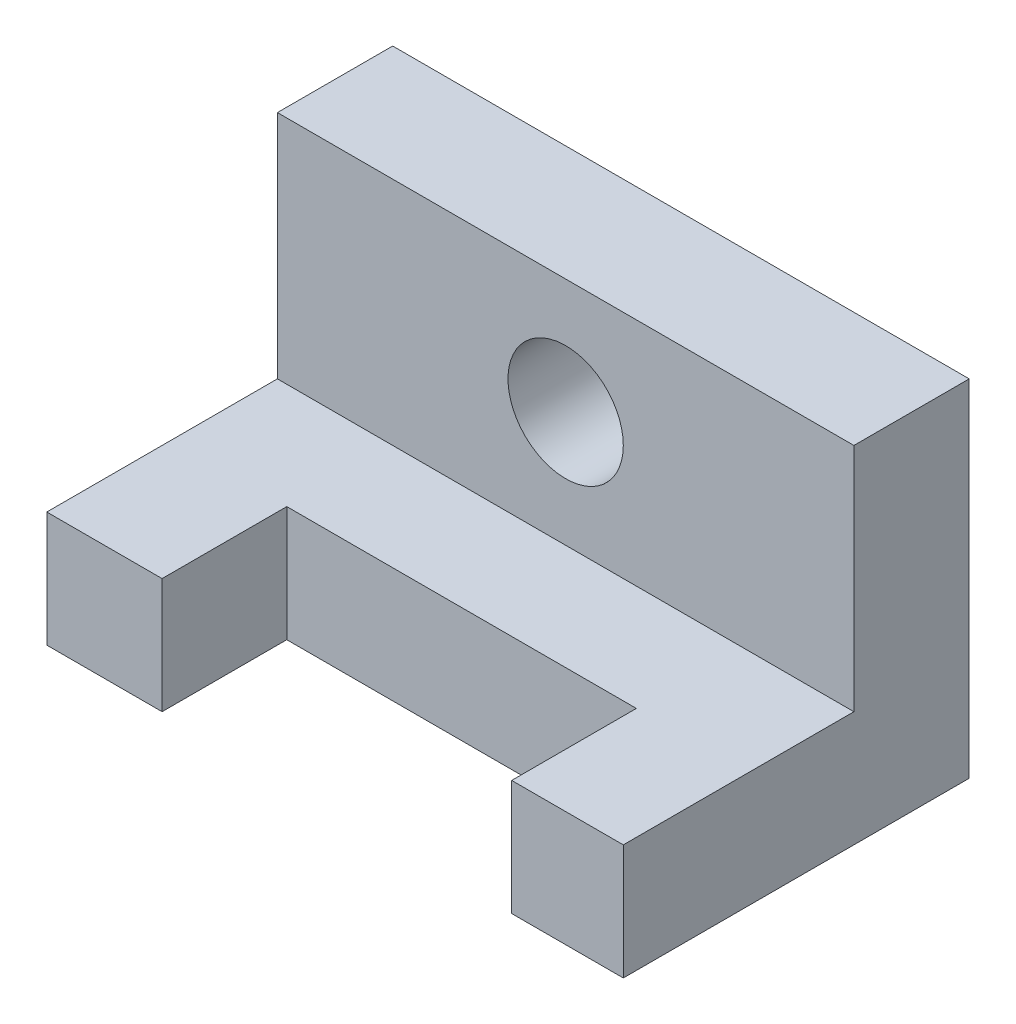
SolidWorks part; units mm, degrees
material "1060 Alloy"
ref_plane "Front Plane" through (0, 0, 0) normal (0, 0, 1) x (1, 0, 0)
ref_plane "Top Plane" through (0, 0, 0) normal (0, 1, 0) x (1, 0, 0)
ref_plane "Right Plane" through (0, 0, 0) normal (1, 0, 0) x (0, 0, -1)
sketch "Sketch1" plane through (0, 0, 0) normal (1, 0, 0) x (0, 0, -1)
  line L1 (0, 0) -> (-1524, 0)
  line L2 (0, 0) -> (0, 1524)
  line L3 (0, 1524) -> (-508, 1524)
  line L4 (-1524, 0) -> (-1524, 508)
  line L7 (-1524, 508) -> (-508, 508)
  line L8 (-508, 1524) -> (-508, 508)
  dimension "D1" = 1524
  dimension "D2" = 1524
  dimension "D3" = 1016
  dimension "D4" = 1016
extrude "Boss-Extrude1" add sketch "Sketch1" along normal blind 2540
sketch "Sketch2" plane through (0, 0, 0) normal (0, 1, 0) x (1, 0, 0)
  line L0 (2540, -1524) -> (0, -1524) construction
  line L1 (508, -974.657) -> (2048.2343, -974.657)
  line L2 (508, -974.657) -> (508, -1524)
  line L3 (508, -1524) -> (2048.2343, -1524)
  line L4 (2048.2343, -974.657) -> (2048.2343, -1524)
  line L5 (0, -508) -> (0, -1524) construction
  dimension "D1" = 549.343
  dimension "D2" = 508
extrude "Cut-Extrude1" cut sketch "Sketch2" along normal blind 508
sketch "Sketch3" plane through (0, 0, 0) normal (0, 0, 1) x (1, 0, 0)
  line L0 (0, 1524) -> (0, 508) construction
  line L1 (2540, 1524) -> (0, 1524) construction
  circle A0 centre (1270, 1016) radius 254
  dimension "D1" = 1270
  dimension "D3" = 508
  dimension "D2" = 508
extrude "Cut-Extrude2" cut sketch "Sketch3" along normal blind 508
